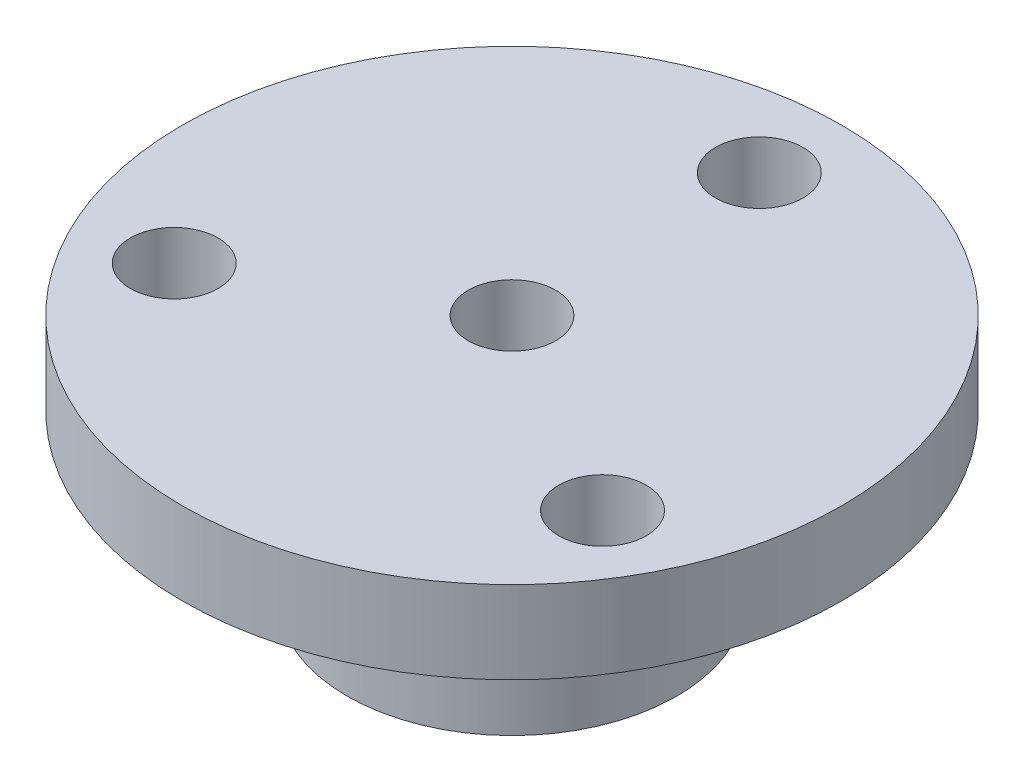
SolidWorks part; units mm, degrees
ref_plane "Front Plane" through (0, 0, 0) normal (0, 0, 1) x (1, 0, 0)
ref_plane "Top Plane" through (0, 0, 0) normal (0, 1, 0) x (1, 0, 0)
ref_plane "Right Plane" through (0, 0, 0) normal (1, 0, 0) x (0, 0, -1)
sketch "Sketch1" plane through (0, 0, 0) normal (0, 1, 0) x (1, 0, 0)
  circle A0 centre (0, 0) radius 12.7
  dimension "D1" = 25.4
extrude "Boss-Extrude1" add sketch "Sketch1" along normal blind 12.7
sketch "Sketch2" plane through (0, 12.7, 0) normal (0, 1, 0) x (1, 0, 0)
  circle A0 centre (0, 0) radius 25.4
  dimension "D1" = 50.8
extrude "Boss-Extrude2" add sketch "Sketch2" along normal blind 6.35
sketch "Sketch3" plane through (0, 19.05, 0) normal (0, 1, 0) x (1, 0, 0)
  line L0 (0, 0) -> (0, 25.4) construction
  line L1 (0, 0) -> (25.4, 0) construction
  circle A0 centre (0, 0) radius 3.3734
  circle A1 centre (0, 0) radius 25.4 construction
  dimension "D1" = 6.7469
extrude "Cut-Extrude1" cut sketch "Sketch3" against normal through all
hole_wizard "H (0.266) Diameter Hole1" positions "Sketch5" profile "Sketch6" hole size "H" standard "ANSI Inch"
sketch "Sketch5" plane through (0, 19.05, 0) normal (0, 1, 0) x (1, 0, 0)
  line L0 (0, 0) -> (0, 25.4) construction
  line L4 (0, 0) -> (-21.997, -12.7) construction
  line L5 (0, 0) -> (21.997, -12.7) construction
  circle A0 centre (0, 0) radius 25.4 construction
  point P17 (0, 19.05)
  point P50 (-16.4978, -9.525)
  point P52 (16.4978, -9.525)
  dimension "D1" = 19.05
  dimension "D2" = 120
  dimension "D3" = 120
  dimension "D4" = 19.05
  dimension "D5" = 19.05
sketch "Sketch6" plane through (0, 19.05, -19.05) normal (1, 0, 0) x (0, 0, 1)
  line L0 (0, 0) -> (0, 27.4298)
  line L1 (0, 27.4298) -> (3.3782, 25.4)
  line L2 (3.3782, 25.4) -> (3.3782, 0)
  line L5 (3.3782, 0) -> (0, 0)
  line L10 (0, 27.4298) -> (-3.3782, 25.4) construction
  line L11 (0, -6.35) -> (0, 107.95) construction
  dimension "Hole Dia." = 6.7564
  dimension "Hole Depth" = 25.4
  dimension "Drill Angle" = 118
hole_wizard "#10 (0.1935) Diameter Hole1" positions "Sketch9" profile "Sketch8" hole size "#10" standard "ANSI Inch"
sketch "Sketch9" plane through (0, 0, 0) normal (0, 0, 1) x (1, 0, 0)
  line L0 (0, 0) -> (0, 20.0457) construction
  point P12 (0, 6.35)
  dimension "D1" = 6.35
sketch "Sketch8" plane through (0, 6.35, 0) normal (1, 0, 0) x (0, 1, 0)
  line L0 (0, 0) -> (0, 26.8766)
  line L1 (0, 26.8766) -> (2.4574, 25.4)
  line L2 (2.4574, 25.4) -> (2.4574, 0)
  line L5 (2.4574, 0) -> (0, 0)
  line L10 (0, 26.8766) -> (-2.4575, 25.4) construction
  line L11 (0, -6.35) -> (0, 107.95) construction
  dimension "Hole Dia." = 4.9149
  dimension "Hole Depth" = 25.4
  dimension "Drill Angle" = 118
